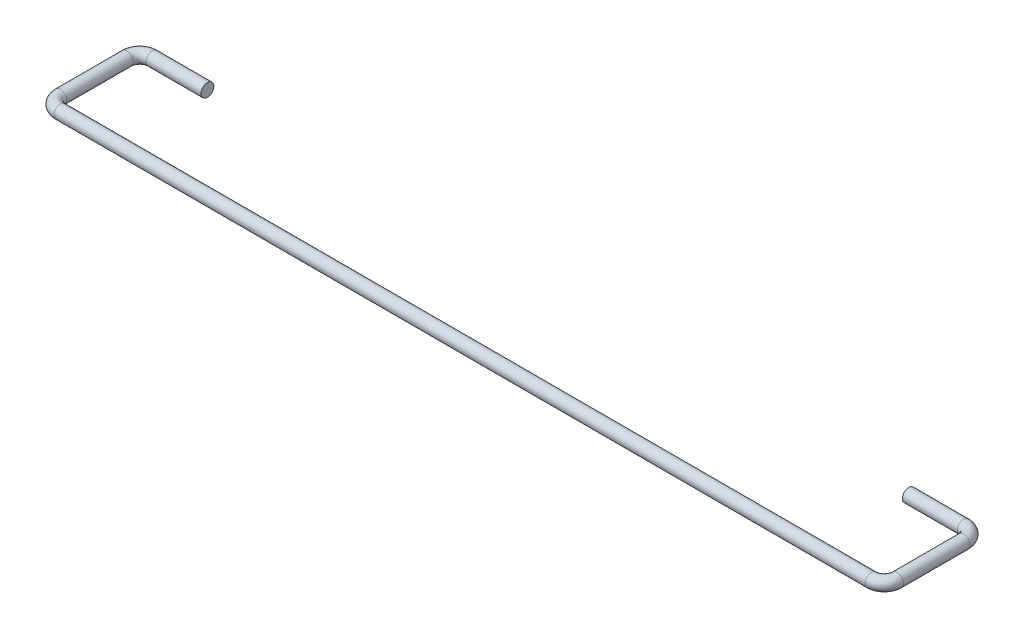
SolidWorks part; units mm, degrees
ref_plane "Front Plane" through (0, 0, 0) normal (0, 0, 1) x (1, 0, 0)
ref_plane "Top Plane" through (0, 0, 0) normal (0, 1, 0) x (1, 0, 0)
ref_plane "Right Plane" through (0, 0, 0) normal (1, 0, 0) x (0, 0, -1)
sketch "Path" plane through (0, 0, 0) normal (0, 1, 0) x (1, 0, 0)
  line L0 (-43.75, -994.1483) -> (-43.75, 49005.8517) construction
  line L1 (-50.6, 11.5) -> (-43.75, 11.5)
  line L2 (-52.2, 9.9) -> (-52.2, 1.6)
  line L3 (-50.6, 0) -> (50.6, 0)
  line L4 (52.2, 9.9) -> (52.2, 1.6)
  line L5 (-52.2, 11.5) -> (52.2, 0) construction
  line L6 (-52.2, 0) -> (52.2, 11.5) construction
  line L7 (43.75, -994.429) -> (43.75, 49005.571) construction
  line L8 (-1000, 5.75) -> (49000, 5.75) construction
  line L9 (0, -995.1) -> (0, 49004.9) construction
  line L10 (43.75, 11.5) -> (50.6, 11.5)
  arc A0 (50.6, 11.5) -> (52.2, 9.9) centre (50.6, 9.9) cw
  arc A1 (50.6, 0) -> (52.2, 1.6) centre (50.6, 1.6) ccw
  arc A2 (-52.2, 1.6) -> (-50.6, 0) centre (-50.6, 1.6) ccw
  arc A3 (-50.6, 11.5) -> (-52.2, 9.9) centre (-50.6, 9.9) ccw
  point P0 (0, 5.75)
  point P11 (-43.75, 5.75)
  point P13 (43.75, 5.75)
  dimension "D4" = 1.6
  dimension "D1" = 11.5
  dimension "D2" = 104.4
  dimension "D3" = 87.5
ref_plane "Plane1" through (-43.75, 0, 0) normal (1, 0, 0) x (0, 0, -1)
sketch "Segment" plane through (-43.75, 0, 0) normal (1, 0, 0) x (0, 0, -1)
  line L0 (-200994.1483, 0) -> (249005.8517, 0) construction
  circle A0 centre (11.5, 0) radius 0.8
  dimension "D1" = 1.6
sweep "Wire" add profiles "Segment" path "Path"
